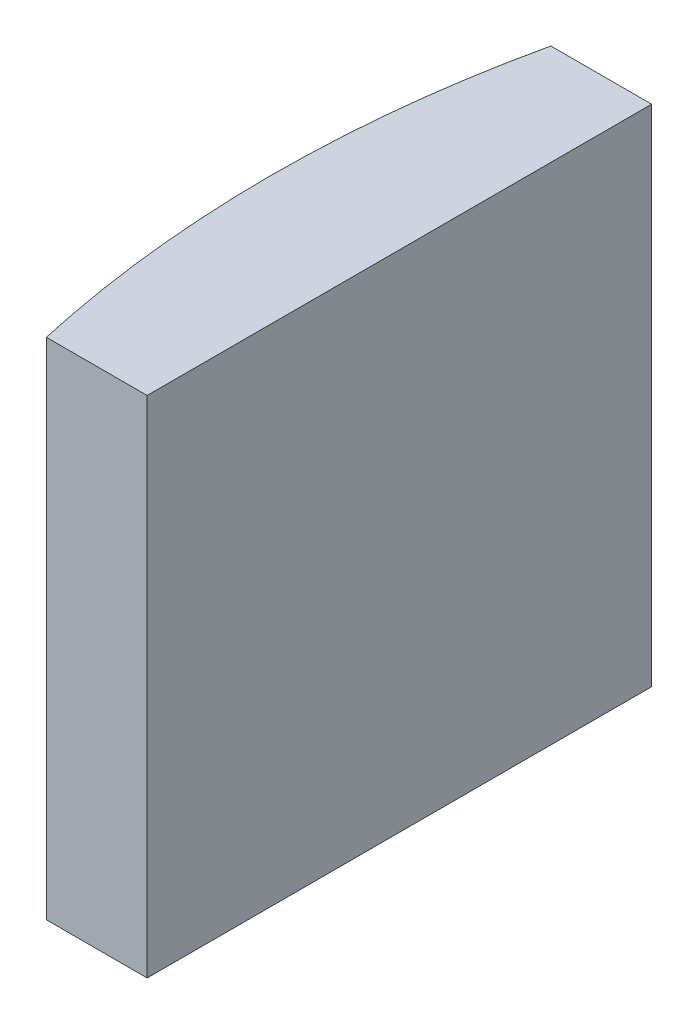
SolidWorks part; units mm, degrees
ref_plane "前视基准面" through (0, 0, 0) normal (0, 0, 1) x (1, 0, 0)
ref_plane "上视基准面" through (0, 0, 0) normal (0, 1, 0) x (1, 0, 0)
ref_plane "右视基准面" through (0, 0, 0) normal (1, 0, 0) x (0, 0, -1)
sketch "草图1" plane through (0, 0, 0) normal (0, 1, 0) x (1, 0, 0)
  line L0 (-23.3839, 0) -> (10.8051, 0) construction
  line L1 (-18.0128, 5) -> (-16.0148, 5)
  line L2 (-18.0128, -5) -> (-16.0148, -5)
  line L3 (-16.0148, 5) -> (-16.0148, -5)
  arc A0 (-18.0128, 5) -> (-18.0128, -5) centre (4.3552, 0) ccw
  point P2 (-18.5648, 0)
  point P4 (-16.0148, 0)
  dimension "D2" = 5
  dimension "D3" = 22.92
  dimension "D4" = 2.55
  dimension "D1" = 5
extrude "凸台-拉伸1" add sketch "草图1" along normal blind 10
